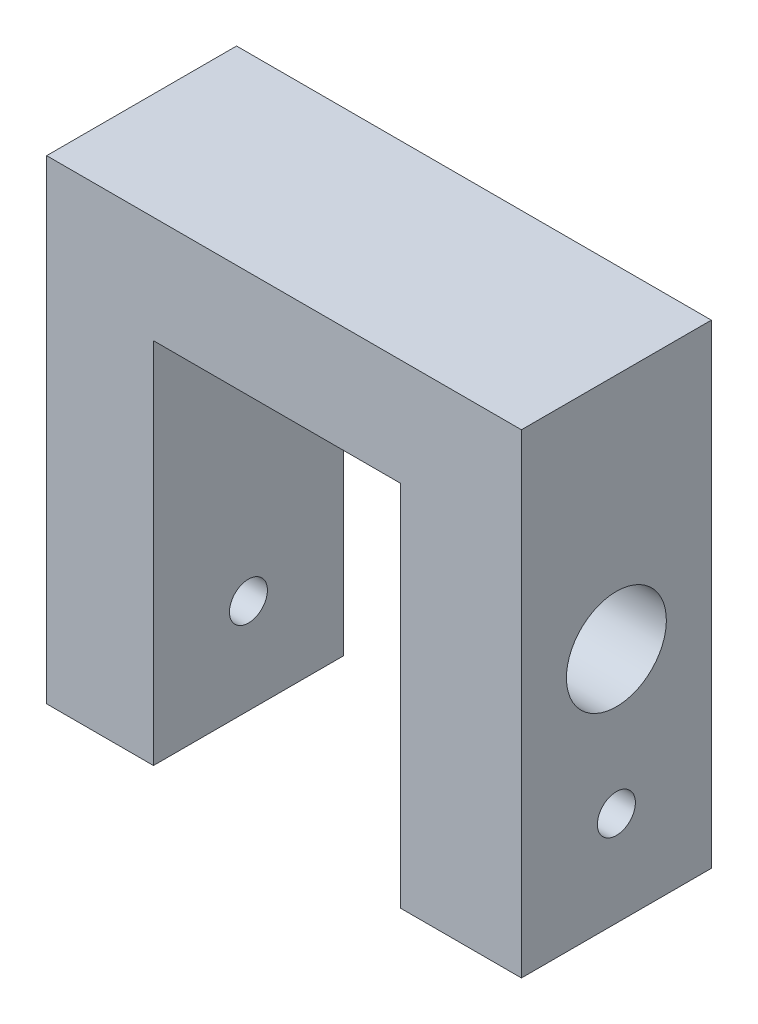
SolidWorks part; units mm, degrees
ref_plane "前视基准面" through (0, 0, 0) normal (0, 0, 1) x (1, 0, 0)
ref_plane "上视基准面" through (0, 0, 0) normal (0, 1, 0) x (1, 0, 0)
ref_plane "右视基准面" through (0, 0, 0) normal (1, 0, 0) x (0, 0, -1)
sketch "草图2" plane through (0, 0, 0) normal (0, 0, 1) x (1, 0, 0)
  line L0 (-20, -20) -> (-20, 20)
  line L1 (-20, 20) -> (20, 20)
  line L2 (20, 20) -> (20, -20)
  line L3 (20, -20) -> (9.8, -20)
  line L4 (9.8, -20) -> (9.8, 11)
  line L5 (9.8, 11) -> (-11, 11)
  line L6 (-11, 11) -> (-11, -20)
  line L7 (-11, -20) -> (-20, -20)
extrude "凸台-拉伸2" add sketch "草图2" along normal blind 16
sketch "草图3" plane through (20, 0, 0) normal (1, 0, 0) x (0, 0, -1)
  circle A0 centre (-8, 0) radius 4.21
extrude "切除-拉伸1" cut sketch "草图3" against normal blind 11
sketch "草图5" plane through (20, 0, 0) normal (1, 0, 0) x (0, 0, -1)
  circle A0 centre (-8, -12) radius 1.6
extrude "切除-拉伸2" cut sketch "草图5" against normal blind 40
